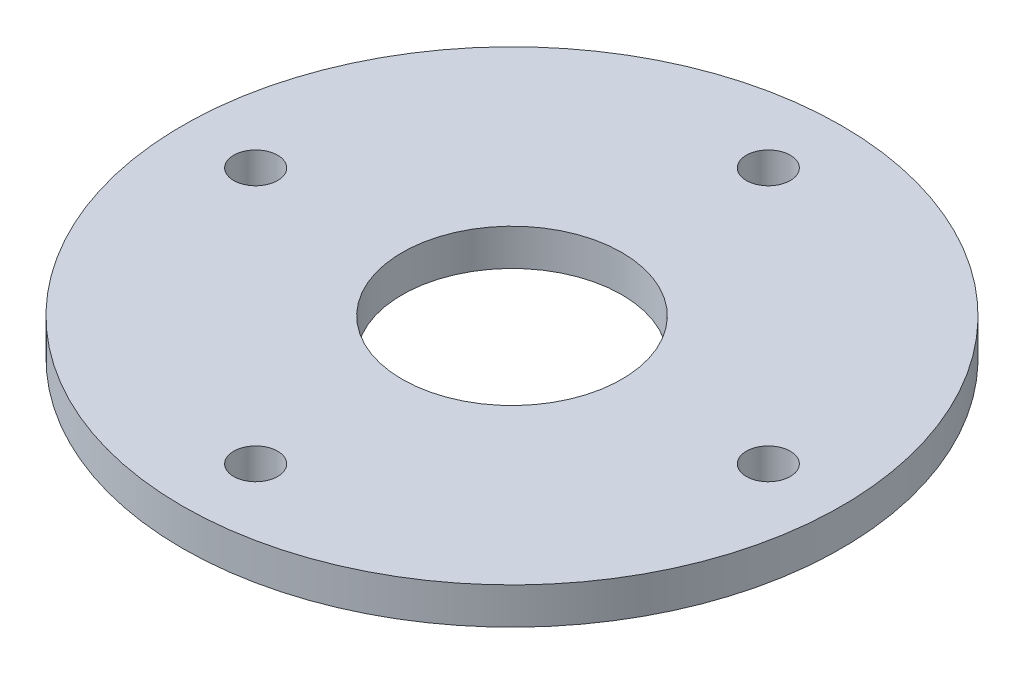
SolidWorks part; units mm, degrees
ref_plane "前基準面" through (0, 0, 0) normal (0, 0, 1) x (1, 0, 0)
ref_plane "上基準面" through (0, 0, 0) normal (0, 1, 0) x (1, 0, 0)
ref_plane "右基準面" through (0, 0, 0) normal (1, 0, 0) x (0, 0, -1)
sketch "草圖1" plane through (0, 0, 0) normal (0, 1, 0) x (1, 0, 0)
  line L0 (0, 0) -> (0, 75.702) construction
  line L1 (0, 75.702) -> (0, -85.4399) construction
  line L2 (0, 0) -> (137.2261, 0) construction
  line L3 (137.2261, 0) -> (-111.8072, 0) construction
  circle A0 centre (0, 0) radius 15
  circle A1 centre (0, 0) radius 45
  circle A2 centre (0, 35) radius 3
  circle A3 centre (0, -35) radius 3
  circle A4 centre (35, 0) radius 3
  circle A5 centre (-35, 0) radius 3
  dimension "D1" = 30
  dimension "D2" = 90
  dimension "D7" = 6
  dimension "D8" = 6
  dimension "D9" = 6
  dimension "D10" = 6
  dimension "D3" = 35
  dimension "D4" = 35
  dimension "D5" = 35
  dimension "D6" = 35
extrude "填料-伸長3" add sketch "草圖1" along normal blind 5 contours A1 A5 A4 A3 A2 A0
